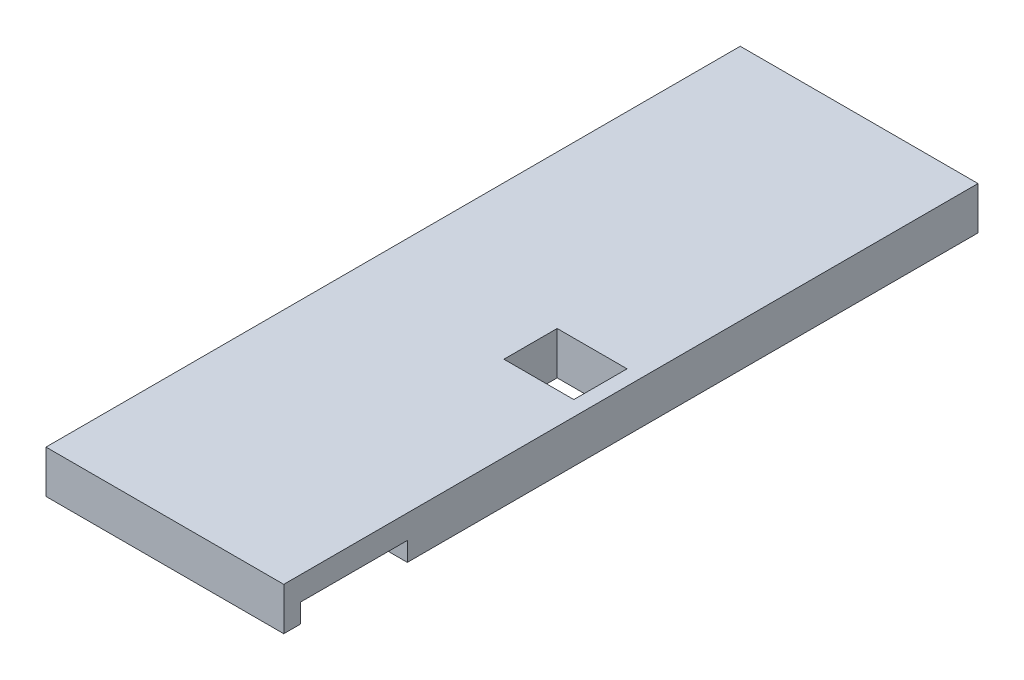
SolidWorks part; units mm, degrees
ref_plane "Front Plane" through (0, 0, 0) normal (0, 0, 1) x (1, 0, 0)
ref_plane "Top Plane" through (0, 0, 0) normal (0, 1, 0) x (1, 0, 0)
ref_plane "Right Plane" through (0, 0, 0) normal (1, 0, 0) x (0, 0, -1)
sketch "Sketch1" plane through (0, 0, 0) normal (0, 1, 0) x (1, 0, 0)
  line L1 (-50, -146) -> (50, -146)
  line L2 (-50, -146) -> (-50, 146)
  line L3 (-50, 146) -> (50, 146)
  line L4 (50, -146) -> (50, 146)
  line L5 (-50, -146) -> (50, 146) construction
  line L6 (-50, 146) -> (50, -146) construction
  point P0 (0, 0)
  dimension "D1" = 100
  dimension "D2" = 292
extrude "Boss-Extrude1" add sketch "Sketch1" along normal mid plane 18
sketch "Sketch2" plane through (0, -9, 0) normal (0, -1, 0) x (1, 0, 0)
  line L0 (29, 17.7) -> (29, -4.7) construction
  line L1 (43.7, 6.5) -> (14.3, 6.5) construction
  line L2 (50, -146) -> (-50, -146) construction
  line L3 (50, 146) -> (50, -146) construction
  line L8 (43.7, -4.7) -> (43.7, 17.7)
  line L9 (43.7, 17.7) -> (14.3, 17.7)
  line L10 (14.3, 17.7) -> (14.3, -4.7)
  line L11 (14.3, -4.7) -> (43.7, -4.7)
  dimension "D1" = 29.4
  dimension "D2" = 22.4
  dimension "D3" = 152.5
  dimension "D4" = 21
extrude "Cut-Extrude1" cut sketch "Sketch2" against normal through all
sketch "Sketch3" plane through (0, -9, 0) normal (0, -1, 0) x (1, 0, 0)
  line L0 (50, 146) -> (50, -146) construction
  line L1 (36.5, 94.0211) -> (50, 94.0211)
  line L2 (36.5, 94.0211) -> (36.5, 139.0211)
  line L3 (36.5, 139.0211) -> (50, 139.0211)
  line L4 (50, 94.0211) -> (50, 139.0211)
  line L6 (-50, 146) -> (50, 146) construction
  dimension "D1" = 6.9789
  dimension "D2" = 45
  dimension "D3" = 13.5
extrude "Cut-Extrude2" cut sketch "Sketch3" against normal blind 8
